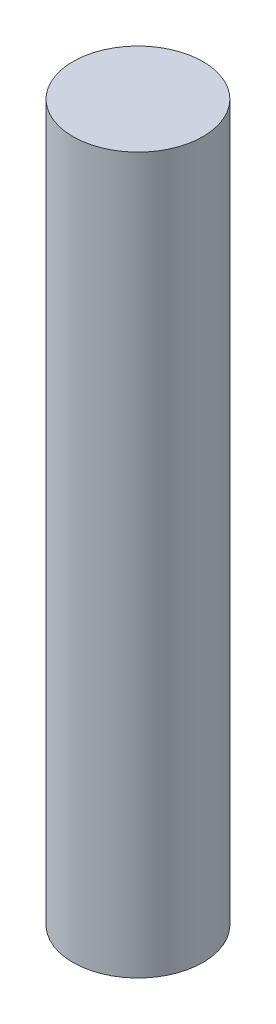
SolidWorks part; units mm, degrees
material "6061-T4 (SS)"
ref_plane "Front Plane" through (0, 0, 0) normal (0, 0, 1) x (1, 0, 0)
ref_plane "Top Plane" through (0, 0, 0) normal (0, 1, 0) x (1, 0, 0)
ref_plane "Right Plane" through (0, 0, 0) normal (1, 0, 0) x (0, 0, -1)
sketch "Sketch1" plane through (0, 0, 0) normal (0, 1, 0) x (1, 0, 0)
  circle A0 centre (0, 0) radius 10
  dimension "D1" = 20
extrude "Boss-Extrude1" add sketch "Sketch1" along normal blind 110
equation "\"D1@Boss-Extrude1\" = 110.00mm"
